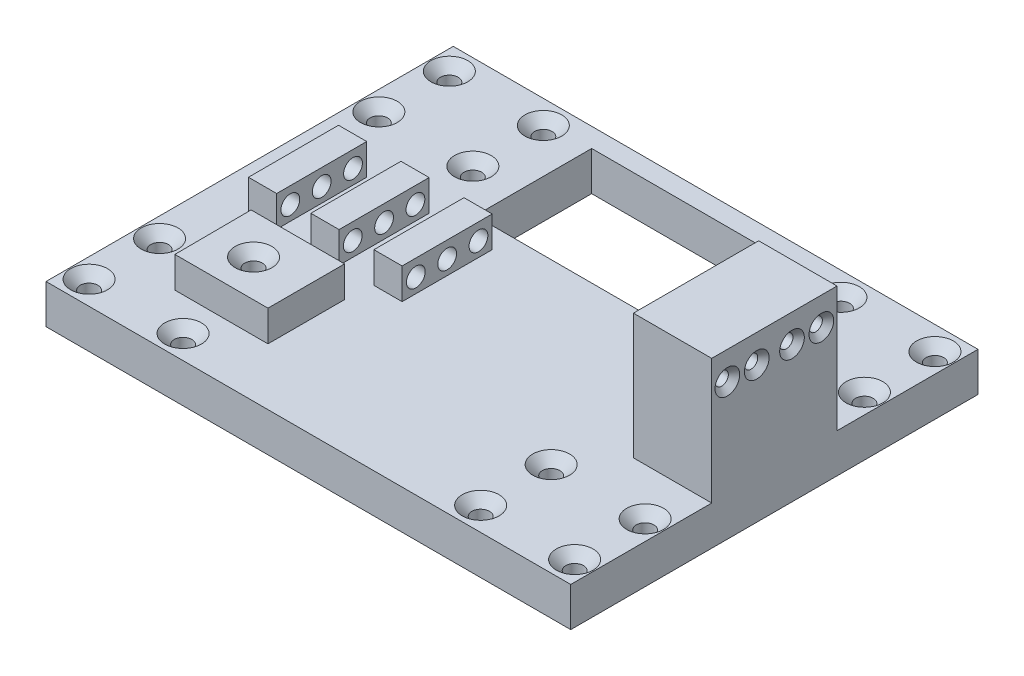
SolidWorks part; units mm, degrees
ref_plane "Front Plane" through (0, 0, 0) normal (0, 0, 1) x (1, 0, 0)
ref_plane "Top Plane" through (0, 0, 0) normal (0, 1, 0) x (1, 0, 0)
ref_plane "Right Plane" through (0, 0, 0) normal (1, 0, 0) x (0, 0, -1)
sketch "Sketch1" plane through (0, 0, 0) normal (0, 1, 0) x (1, 0, 0)
  line L1 (-62.4657, 46.5684) -> (71.5343, 46.5684)
  line L2 (-62.4657, 46.5684) -> (-62.4657, -57.4316)
  line L3 (-62.4657, -57.4316) -> (71.5343, -57.4316)
  line L4 (71.5343, 46.5684) -> (71.5343, -57.4316)
  line B0 (-44.2292, -16.4291) -> (-44.2292, -35.7291)
  line B1 (-44.1292, -35.7291) -> (-44.1292, -16.5291)
  line B2 (-20.2292, 3.0709) -> (-20.2292, 6.5709)
  line B3 (-20.3292, 6.6709) -> (-20.3292, 3.0709)
  line B4 (-44.1292, -12.9291) -> (-44.1292, 3.0709)
  line B5 (-44.2292, 3.0709) -> (-44.2292, -12.9291)
  line B6 (-27.3292, -16.5291) -> (-20.3292, -16.5291)
  line B7 (-28.2292, -16.4291) -> (-28.2292, -12.9291)
  line B8 (-28.1292, -12.9291) -> (-28.1292, 3.0709)
  line B9 (-27.4292, 6.5709) -> (-27.4292, 3.0709)
  line B10 (-27.3292, 6.6709) -> (-20.3292, 6.6709)
  line B11 (-28.2292, 3.0709) -> (-28.2292, 6.5709)
  line B12 (-36.2292, 6.5709) -> (-36.2292, 3.0709)
  line B13 (-37.0292, 6.5709) -> (-36.2292, 6.5709)
  line B14 (-37.1292, 6.6709) -> (-44.1292, 6.6709)
  line B15 (-36.2292, -16.4291) -> (-37.0292, -16.4291)
  line B16 (-37.1292, -16.5291) -> (-44.1292, -16.5291)
  line B17 (-36.2292, -12.9291) -> (-36.2292, -16.4291)
  line B18 (-36.3292, 3.0709) -> (-36.3292, -12.9291)
  line B19 (-20.3292, 3.0709) -> (-20.3292, -12.9291)
  line B20 (-44.1292, 3.0709) -> (-44.1292, 6.6709)
  line B21 (-20.3292, 11.0709) -> (-20.3292, 6.6709)
  line B22 (-35.8292, 14.9709) -> (-28.6292, 14.9709)
  line B23 (-28.6292, 14.6709) -> (-20.3292, 14.6709)
  line B24 (-20.3292, 14.6709) -> (-20.3292, 11.0709)
  line B25 (-44.1292, 6.6709) -> (-44.1292, 11.0709)
  line B26 (-44.1292, 11.0709) -> (-44.1292, 14.6709)
  line B27 (-44.1292, 14.6709) -> (-35.8292, 14.6709)
  line B28 (-28.4657, -57.4316) -> (-28.4657, -27.4316)
  line B29 (-62.4657, -27.4316) -> (-28.4657, -27.4316)
  line B30 (-62.4657, -57.4316) -> (-28.4657, -57.4316)
  line B31 (-62.4657, -57.4316) -> (-62.4657, -27.4316)
  circle B32 centre (-33.4657, -33.4316) radius 2
  circle B33 centre (-33.4657, -51.4316) radius 2
  circle B34 centre (-57.4657, -51.4316) radius 2
  circle B35 centre (-57.4657, -33.4316) radius 2
  line B36 (-28.4657, 16.5684) -> (-28.4657, 46.5684)
  line B37 (-62.4657, 16.5684) -> (-28.4657, 16.5684)
  line B38 (-62.4657, 16.5684) -> (-62.4657, 46.5684)
  circle B39 centre (-33.4657, 40.5684) radius 2
  circle B40 centre (-33.4657, 22.5684) radius 2
  circle B41 centre (-57.4657, 22.5684) radius 2
  circle B42 centre (-57.4657, 40.5684) radius 2
  line B43 (37.5343, -27.4316) -> (71.5343, -27.4316)
  circle B44 centre (66.5343, -33.4316) radius 2
  circle B45 centre (66.5343, -51.4316) radius 2
  circle B46 centre (42.5343, -51.4316) radius 2
  circle B47 centre (42.5343, -33.4316) radius 2
  line B48 (37.5343, 16.5684) -> (71.5343, 16.5684)
  line B49 (37.5343, 16.5684) -> (37.5343, 46.5684)
  circle B50 centre (66.5343, 40.5684) radius 2
  circle B51 centre (66.5343, 22.5684) radius 2
  circle B52 centre (42.5343, 22.5684) radius 2
  circle B53 centre (42.5343, 40.5684) radius 2
  dimension "D1" = 134
  dimension "D2" = 104
sketch_block_instance "Block-SMALLMOTORBOTTOM-1"
sketch_block "Block-SMALLMOTORBOTTOM"
sketch_block_instance "Block-LinearBearing-6"
sketch_block "Block-LinearBearing"
sketch_block_instance "Block-LinearBearing-8"
sketch_block_instance "Block-LinearBearing-9"
sketch_block_instance "Block-LinearBearing-10"
sketch "Sketch2" plane through (0, 0, 0) normal (0, 1, 0) x (1, 0, 0)
  line L0 (-62.4657, 46.5684) -> (-62.4657, -57.4316) construction
  line L1 (-62.4657, 46.5684) -> (-62.4657, -57.4316)
  line L2 (-62.4657, -57.4316) -> (71.5343, -57.4316) construction
  line L3 (71.5343, 46.5684) -> (71.5343, -57.4316) construction
  line L4 (-62.4657, 46.5684) -> (71.5343, 46.5684) construction
  line L5 (-62.4657, -57.4316) -> (71.5343, -57.4316)
  line L6 (71.5343, 46.5684) -> (71.5343, -57.4316)
  line L7 (-62.4657, 46.5684) -> (71.5343, 46.5684)
extrude "Boss-Extrude1" add sketch "Sketch2" along normal blind 10
sketch "Sketch3" plane through (0, 10, 0) normal (0, 1, 0) x (1, 0, 0)
  line L1 (-51.7693, -16.4291) -> (-44.5693, -16.4291)
  line L3 (-51.7693, -1.1031) -> (-51.7693, -17.1031)
  line L4 (-44.5693, -17.1031) -> (-44.5693, -1.1031)
  line L5 (-44.5693, -1.1031) -> (-44.5693, 6.5709)
  line L7 (-28.2292, 3.0709) -> (-28.2292, 6.5709) construction
  line L9 (-27.3292, 6.6709) -> (-20.3292, 6.6709) construction
  line L10 (-36.2292, 6.5709) -> (-36.2292, 3.0709) construction
  line L11 (-51.7693, 6.5709) -> (-44.5693, 6.5709)
  line L12 (-35.8292, -1.1031) -> (-35.8292, -17.1031)
  line L13 (-28.6292, -17.1031) -> (-28.6292, -1.1031)
  line L14 (-35.8292, 6.5709) -> (-28.6292, 6.5709)
  line L15 (-35.8292, -16.4291) -> (-28.6292, -16.4291)
  line L16 (-35.8292, -17.1031) -> (-35.8292, -16.4291)
  line L17 (-28.6292, -17.1031) -> (-28.6292, -16.4291)
  line L18 (-35.8292, -1.1031) -> (-35.8292, 6.5709)
  line L19 (-28.6292, -1.1031) -> (-28.6292, 6.5709)
  line L20 (-37.1292, -16.5291) -> (-44.1292, -16.5291) construction
  line L53 (-51.7693, -1.1031) -> (-51.7693, 6.5709)
  line L54 (-19.729, -16.4291) -> (-12.529, -16.4291)
  line L55 (-19.729, -1.1031) -> (-19.729, -17.1031)
  line L56 (-12.529, -17.1031) -> (-12.529, -1.1031)
  line L57 (-12.529, -1.1031) -> (-12.529, 6.5709)
  line L58 (-19.729, 6.5709) -> (-12.529, 6.5709)
  line L59 (-19.729, -1.1031) -> (-19.729, 6.5709)
  dimension "D1" = 0.4
  dimension "D2" = 0.1
  dimension "D3" = 0.4
  dimension "D4" = 0.1
extrude "Boss-Extrude2" add sketch "Sketch3" along normal blind 7.9 contours L13 L19 L14 L18 L12 L15 | L53 L3 L1 L4 L5 L11 | L59 L55 L54 L56 L57 L58
sketch "Sketch4" plane through (-51.7693, 0, 0) normal (-1, 0, 0) x (0, 0, 1)
  line L0 (-6.5709, 17.9) -> (16.4291, 17.9)
  line L4 (4.9291, 17.9) -> (4.9291, 8.7762) construction
  line L8 (-46.5684, 10) -> (57.4316, 10) construction
  point P1 (4.9291, 17.9)
  line B0 (-3.0709, 16.8) -> (12.9291, 16.8)
  line B1 (-3.0709, 10.6) -> (12.9291, 10.6)
  circle B2 centre (12.9291, 13.7) radius 2.4
  circle B3 centre (4.9291, 13.7) radius 2.4
  circle B4 centre (-3.0709, 13.7) radius 2.4
  arc B5 (-3.0709, 16.8) -> (-3.0709, 10.6) centre (-3.0709, 13.7) ccw
  arc B6 (12.9291, 10.6) -> (12.9291, 16.8) centre (12.9291, 13.7) ccw
  dimension "D1" = 0.6
sketch_block_instance "Block-3HolePiece-4"
sketch_block "Block-3HolePiece"
sketch "Sketch5" plane through (0, 10, 0) normal (0, 1, 0) x (1, 0, 0)
  line L0 (-20.3292, -16.5291) -> (-20.3292, -42.8873)
  line L1 (-20.3292, -42.8873) -> (-44.1002, -42.8873)
  line L2 (-44.1002, -42.8873) -> (-44.2292, -16.4291)
  line L4 (-44.1956, -23.3195) -> (-20.3292, -23.3195)
extrude "Boss-Extrude3" add sketch "Sketch5" along normal up to surface (7.9 mm away) contours L4 L2 L1 L0 up to face at (-32.2292, 17.9, 4.9291)
hole_wizard "CSK for M4 Flat Head Machine Screw1" positions "Sketch6" profile "Sketch7" countersink size "M4" standard "ANSI Metric"
sketch "Sketch6" plane through (0, 10, 0) normal (0, 1, 0) x (1, 0, 0)
  point P56 (-57.4657, 40.5684)
  point P59 (-33.4657, 40.5684)
  point P62 (-57.4657, 22.5684)
  point P65 (-33.4657, 22.5684)
  point P68 (-57.4657, -33.4316)
  point P74 (-57.4657, -51.4316)
  point P77 (-33.4657, -51.4316)
  point P80 (42.5343, -33.4316)
  point P83 (66.5343, -33.4316)
  point P86 (42.5343, -51.4316)
  point P89 (66.5343, -51.4316)
  point P92 (42.5343, 40.5684)
  point P95 (66.5343, 40.5684)
  point P98 (66.5343, 22.5684)
  point P101 (42.5343, 22.5684)
sketch "Sketch7" plane through (-57.4657, 10, -40.5684) normal (1, 0, 0) x (0, 0, 1)
  line L0 (0, 0) -> (0, 11.3519)
  line L1 (0, 11.3519) -> (2.25, 10)
  line L2 (2.25, 10) -> (2.25, 2.45)
  line L3 (2.25, 2.45) -> (4.7, 0)
  line L5 (4.7, 0) -> (0, 0)
  line L6 (-2.25, 2.45) -> (-4.7, 0) construction
  line L10 (0, 11.3519) -> (-2.25, 10) construction
  line L11 (0, -6.35) -> (0, 107.95) construction
  dimension "Hole Dia." = 4.5
  dimension "Hole Depth" = 10
  dimension "Near C'Sink Dia." = 9.4
  dimension "Near C'Sink Angle" = 90
  dimension "Drill Angle" = 118
extrude "Cut-Extrude3" cut sketch "Sketch4" along direction (-1, 0, 0) on the side against the normal through all contours B4 | L4 B3 | B3 L4 | B2
sketch "Sketch8" plane through (0, 10, 0) normal (0, 1, 0) x (1, 0, 0)
  line L0 (71.5343, 46.5684) -> (71.5343, -57.4316) construction
  line L1 (71.5343, -21.4316) -> (51.5343, -21.4316)
  line L2 (71.5343, -21.4316) -> (71.5343, 10.5684)
  line L3 (71.5343, 10.5684) -> (51.5343, 10.5684)
  line L4 (51.5343, -21.4316) -> (51.5343, 10.5684)
  line L5 (37.5343, 16.5684) -> (71.5343, 16.5684) construction
  line L6 (37.5343, -27.4316) -> (71.5343, -27.4316) construction
  dimension "D1" = 20
  dimension "D2" = 6
  dimension "D3" = 6
extrude "Boss-Extrude4" add sketch "Sketch8" along normal blind 32
sketch "Sketch9" plane through (0, 10, 0) normal (0, 1, 0) x (1, 0, 0)
  line L1 (-22.2082, 41.658) -> (26.6164, 41.658)
  line L2 (-22.2082, 41.658) -> (-22.2082, 11.8986)
  line L3 (-22.2082, 11.8986) -> (26.6164, 11.8986)
  line L4 (26.6164, 41.658) -> (26.6164, 11.8986)
  line L5 (-22.2082, 41.658) -> (26.6164, 11.8986) construction
  line L6 (-22.2082, 11.8986) -> (26.6164, 41.658) construction
  circle A0 centre (2.2041, 26.7783) radius 13.5 construction
  dimension "D1" = 27
hole_wizard "CSK for M3 Flat Head Machine Screw1" positions "Sketch12" profile "Sketch11" countersink size "M3" standard "ANSI Metric"
sketch "Sketch12" plane through (71.5343, 0, 0) normal (1, 0, 0) x (0, 0, -1)
  line L0 (-21.4316, 42) -> (10.5684, 42) construction
  line L1 (-21.4316, 42) -> (-21.4316, 10) construction
  line L2 (10.5684, 42) -> (10.5684, 10) construction
  point P0 (-17.4316, 34.83)
  point P2 (-9.9316, 34.83)
  point P4 (-0.9316, 34.83)
  point P6 (6.5684, 34.83)
  dimension "D1" = 7.17
  dimension "D2" = 7.17
  dimension "D3" = 7.17
  dimension "D4" = 7.17
  dimension "D5" = 4
  dimension "D6" = 4
  dimension "D7" = 7.5
  dimension "D8" = 7.5
sketch "Sketch11" plane through (71.5343, 34.83, 17.4316) normal (0, 1, 0) x (0, 0, -1)
  line L0 (0, 0) -> (0, 11.0215)
  line L1 (0, 11.0215) -> (1.7, 10)
  line L2 (1.7, 10) -> (1.7, 1.45)
  line L3 (1.7, 1.45) -> (3.15, 0)
  line L5 (3.15, 0) -> (0, 0)
  line L6 (-1.7, 1.45) -> (-3.15, 0) construction
  line L10 (0, 11.0215) -> (-1.7, 10) construction
  line L11 (0, -6.35) -> (0, 107.95) construction
  dimension "Hole Dia." = 3.4
  dimension "Hole Depth" = 10
  dimension "Near C'Sink Dia." = 6.3
  dimension "Near C'Sink Angle" = 90
  dimension "Drill Angle" = 118
hole_wizard "CSK for M4 Flat Head Machine Screw2" positions "Sketch15" profile "Sketch14" countersink size "M4" standard "ANSI Metric" end condition through all
sketch "Sketch15" plane through (0, 17.9, 0) normal (0, 1, 0) x (1, 0, 0)
  point P0 (-33.4657, -33.4316)
sketch "Sketch14" plane through (-33.4657, 17.9, 33.4316) normal (1, 0, 0) x (0, 0, 1)
  line L0 (0, 0) -> (0, 17.9)
  line L1 (0, 17.9) -> (2.25, 17.9)
  line L2 (2.25, 17.9) -> (2.25, 2.45)
  line L3 (2.25, 2.45) -> (4.7, 0)
  line L5 (4.7, 0) -> (0, 0)
  line L6 (-2.25, 2.45) -> (-4.7, 0) construction
  line L11 (0, -6.35) -> (0, 107.95) construction
  dimension "Thru Hole Dia." = 4.5
  dimension "Thru Hole Depth" = 17.9
  dimension "Near C'Sink Dia." = 9.4
  dimension "Near C'Sink Angle" = 90
extrude "Cut-Extrude4" cut sketch "Sketch9" against normal through all
